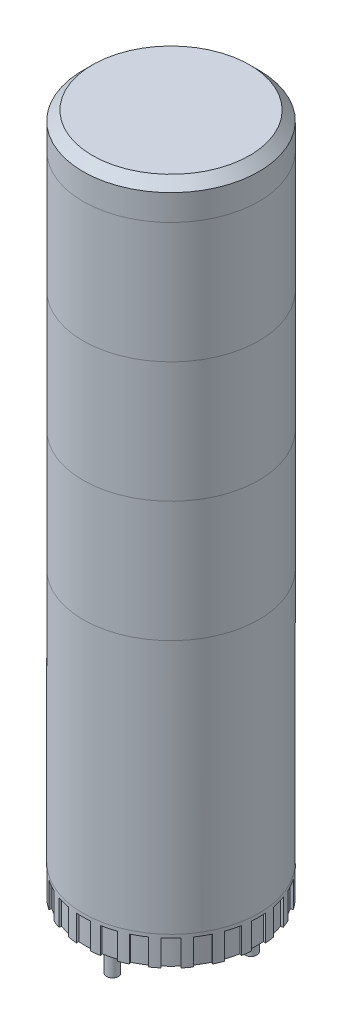
SolidWorks part; units mm, degrees
ref_plane "Front Plane" through (0, 0, 0) normal (0, 0, 1) x (1, 0, 0)
ref_plane "Top Plane" through (0, 0, 0) normal (0, 1, 0) x (1, 0, 0)
ref_plane "Right Plane" through (0, 0, 0) normal (1, 0, 0) x (0, 0, -1)
sketch "Sketch1" plane through (0, 0, 0) normal (0, 1, 0) x (1, 0, 0)
  circle A0 centre (0, 0) radius 30
  dimension "D1" = 60
extrude "Extrude1" add sketch "Sketch1" along normal blind 232.4
ref_plane "Plane1" through (0, 0, 176.0429) normal (0, 0, 1) x (1, 0, 0)
sketch "Sketch2" plane through (0, 0, 176.0429) normal (0, 0, 1) x (1, 0, 0)
  line L0 (-49.3631, 220.4) -> (42.7446, 220.4)
  line L1 (-55.9816, 179.2) -> (56.5331, 179.2) construction
  line L2 (-49.3631, 138.0012) -> (56.5331, 138.0012) construction
  line L3 (-52.6723, 96.8024) -> (49.3631, 96.8024) construction
  line L4 (30, 232.4) -> (-30, 232.4) construction
  dimension "D1" = 12
  dimension "D2" = 41.2
  dimension "D3" = 41.1988
  dimension "D4" = 41.1988
sketch "Sketch3" plane through (0, 0, 176.0429) normal (0, 0, 1) x (1, 0, 0)
  line L0 (-55.9816, 179.2) -> (56.5331, 179.2) construction
  line L1 (-55.9816, 179.2) -> (56.5331, 179.2)
sketch "Sketch4" plane through (0, 0, 176.0429) normal (0, 0, 1) x (1, 0, 0)
  line L0 (-49.3631, 138.0012) -> (56.5331, 138.0012) construction
  line L1 (-49.3631, 138.0012) -> (56.5331, 138.0012)
sketch "Sketch5" plane through (0, 0, 176.0429) normal (0, 0, 1) x (1, 0, 0)
  line L0 (-52.6723, 96.8024) -> (49.3631, 96.8024) construction
  line L1 (-52.6723, 96.8024) -> (49.3631, 96.8024)
split line "Split Line5"
split line "Split Line6"
split line "Split Line7"
split line "Split Line8"
chamfer "Chamfer1" distance 3.175 angle 45 1 edges at (0, 232.4, 30)
sketch "Sketch6" plane through (0, 0, 176.0429) normal (0, 0, 1) x (1, 0, 0)
  line L0 (-45.778, 10) -> (41.3657, 10)
  line L1 (33, 0) -> (-33, 0) construction
  dimension "D1" = 10
split line "Split Line9"
sketch "Sketch7" plane through (0, 0, 0) normal (0, -1, 0) x (1, 0, 0)
  line L0 (29.9053, 2.3813) -> (29.109, 2.3812)
  line L1 (29.9053, -2.3813) -> (29.109, -2.3813)
  line L2 (61.8831, 0) -> (-61.8831, 0) construction
  circle A1 centre (0, 0) radius 30 construction
  circle A2 centre (0, 0) radius 29.2063
  arc A3 (29.109, -2.3813) -> (29.109, 2.3812) centre (0, 0) ccw
  arc A4 (29.9053, -2.3813) -> (29.9053, 2.3813) centre (0, 0) ccw
  dimension "D2" = 4.7625
  dimension "D3" = 2.3813
  dimension "D1" = 0.7937
extrude "Cut-Extrude1" cut sketch "Sketch7" against normal blind 8.88
pattern_circular "CirPattern3" count 24 over 360 about axis through (0, 0, 0) along (0, 1, 0) of "Cut-Extrude1"
sketch "Sketch8" plane through (0, 0, 0) normal (0, -1, 0) x (1, 0, 0)
  line L0 (0, -33) -> (0, 33) construction
  line L1 (0, 0) -> (34.641, -20) construction
  line L2 (0, 0) -> (-31.785, -18.3511) construction
  circle A0 centre (0, 0) radius 20 construction
  circle A1 centre (0, 20) radius 2
  circle A2 centre (17.3205, -10) radius 2
  circle A3 centre (-17.3205, -10) radius 2
  dimension "D1" = 40
  dimension "D2" = 120
  dimension "D4" = 4
  dimension "D3" = 120
extrude "Extrude2" add sketch "Sketch8" along normal blind 12.7
cosmetic thread "Cosmetic Thread1" parameters "D1"=12.7, "D2"=3
cosmetic thread "Cosmetic Thread2" parameters "D1"=12.7, "D2"=3
cosmetic thread "Cosmetic Thread3" parameters "D1"=12.7, "D2"=3
